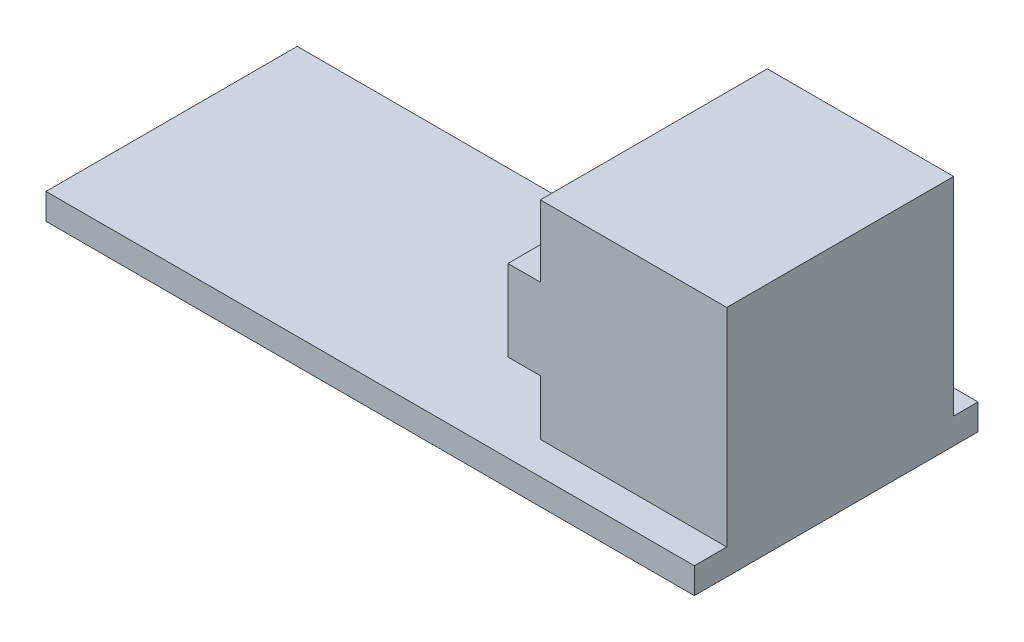
SolidWorks part; units mm, degrees
ref_plane "Front Plane" through (0, 0, 0) normal (0, 0, 1) x (1, 0, 0)
ref_plane "Top Plane" through (0, 0, 0) normal (0, 1, 0) x (1, 0, 0)
ref_plane "Right Plane" through (0, 0, 0) normal (1, 0, 0) x (0, 0, -1)
sketch "Sketch1" plane through (0, 0, 0) normal (0, 1, 0) x (1, 0, 0)
  line L0 (0, 0) -> (0, 15.5)
  line L1 (0, 15.5) -> (26, 15.5)
  line L2 (26, 15.5) -> (26, 17.5)
  line L3 (26, 17.5) -> (40, 17.5)
  line L4 (40, 17.5) -> (40, 0)
  line L5 (40, 0) -> (0, 0)
  dimension "D1" = 40
  dimension "D2" = 17.5
  dimension "D3" = 15.5
  dimension "D4" = 14
extrude "Boss-Extrude1" add sketch "Sketch1" along normal blind 1.6
ref_plane "Plane1" through (0, 0, -16) normal (0, 0, -1) x (-1, 0, 0)
sketch "Sketch2" plane through (0, 0, -16) normal (0, 0, -1) x (-1, 0, 0)
  line L0 (-40, 1.6) -> (-28.5, 1.6)
  line L1 (-28.5, 1.6) -> (-28.5, 5)
  line L2 (-28.5, 5) -> (-26.5, 5)
  line L3 (-26.5, 5) -> (-26.5, 10)
  line L4 (-26.5, 10) -> (-28.5, 10)
  line L5 (-28.5, 10) -> (-28.5, 14.4)
  line L6 (-28.5, 14.4) -> (-40, 14.4)
  line L7 (-40, 14.4) -> (-40, 1.6)
  dimension "D1" = 12.8
  dimension "D2" = 11.5
  dimension "D3" = 4.4
  dimension "D4" = 5
  dimension "D5" = 2
extrude "Boss-Extrude2" add sketch "Sketch2" against normal blind 14
